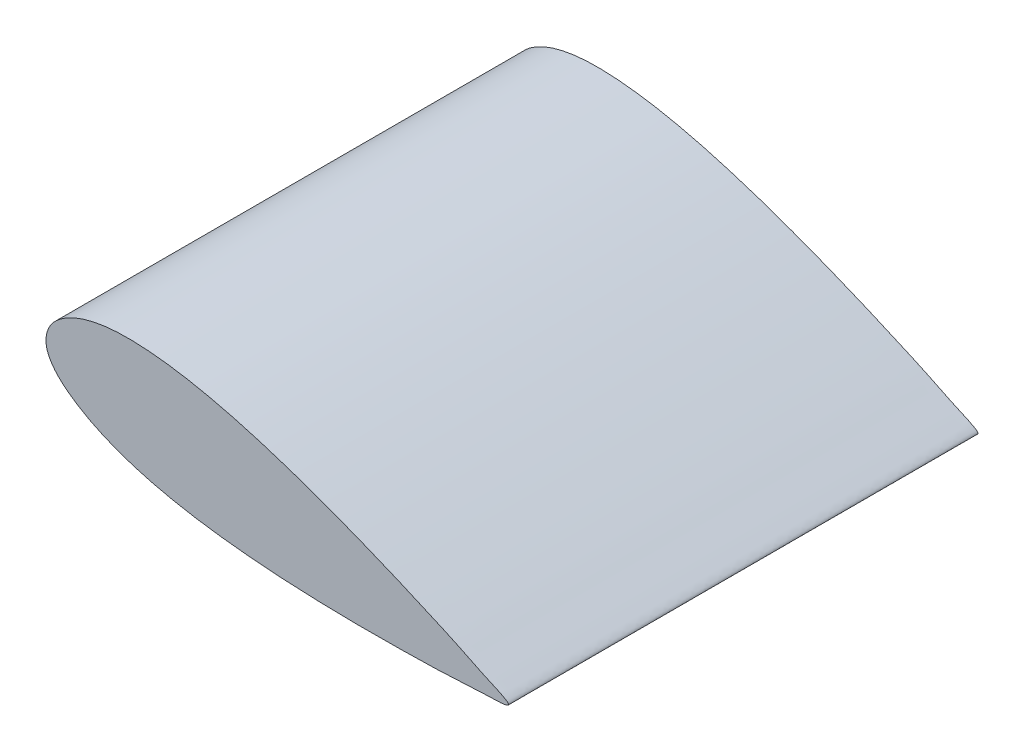
SolidWorks part; units mm, degrees
ref_plane "Front Plane"
ref_plane "Top Plane" through (0, 0, 0) normal (0, 1, 0) x (1, 0, 0)
ref_plane "Right Plane" through (0, 0, 0) normal (1, 0, 0) x (0, 0, -1)
curve "Krzywa1"
  spline degree 3 poles (0.9428, -0.0156, 0) (1.0287, -0.0006, 0) (0.9435, 0.0181, 0) (0.8883, 0.0354, 0) (0.8001, 0.0574, 0) (0.7023, 0.0802, 0) (0.6022, 0.1006, 0) (0.5027, 0.1176, 0) (0.4028, 0.1303, 0) (0.3194, 0.1358, 0) (0.2526, 0.1358, 0) (0.2015, 0.1329, 0) (0.1483, 0.1261, 0) (0.1024, 0.1145, 0) (0.0652, 0.0989, 0) (0.0372, 0.0821, 0) (0.0154, 0.0621, 0) (-0.0018, 0.0351, 0) (-0.005, -0.0015, 0) (0.0163, -0.0292, 0) (0.0392, -0.0467, 0) (0.0601, -0.0584, 0) (0.0834, -0.0687, 0) (0.1128, -0.0792, 0) (0.1506, -0.0894, 0) (0.198, -0.0977, 0) (0.2473, -0.1027, 0) (0.314, -0.1056, 0) (0.3976, -0.1038, 0) (0.4979, -0.0955, 0) (0.5981, -0.0829, 0) (0.699, -0.067, 0) (0.7977, -0.0485, 0) (0.8869, -0.0304, 0) (0.9428, -0.0156, 0) (1.0287, -0.0006, 0) (0.9435, 0.0181, 0) knots -0.097469 -0.04907 -0.024756 0 0.024751 0.04907 0.097468 0.145589 0.193458 0.241069 0.288432 0.335582 0.359147 0.382782 0.407745 0.434926 0.449379 0.46453 0.480955 0.490565 0.509531 0.528284 0.536925 0.550401 0.562004 0.572912 0.5945 0.61722 0.640856 0.664418 0.71157 0.758924 0.806536 0.854407 0.902531 0.95093 0.975244 1 1.024751 1.04907 1.097468 periodic
sketch "Szkic1" plane through (0, 0, 0) normal (0, 0, 1) x (1, 0, 0)
  spline S1 degree 3 poles (462.879, -89.5272) (506.4684, -89.6246) (466.1671, -73.0204) (440.4954, -59.7028) (398.9448, -41.2005) (352.7598, -21.4647) (305.2614, -2.7545) (257.7187, 14.2543) (209.6552, 29.1661) (169.0459, 39.1549) (136.1543, 44.9567) (110.7769, 47.9282) (83.9682, 49.2125) (60.3497, 47.4932) (40.7121, 43.018) (25.4276, 37.2245) (12.982, 29.2599) (2.1437, 17.4495) (-2.5962, -0.3238) (5.4857, -15.7707) (15.2524, -26.3774) (24.5213, -33.9922) (35.1194, -41.0578) (48.6741, -48.8102) (66.4116, -57.0816) (89.027, -65.3111) (112.8532, -72.0398) (145.4554, -79.2868) (186.7898, -85.6211) (236.8966, -90.2639) (287.3262, -92.7716) (338.3708, -93.6956) (388.5945, -93.1489) (434.0629, -91.9802) (462.879, -89.5272) (506.4684, -89.6246) (466.1671, -73.0204) knots -0.097469 -0.04907 -0.024756 0 0.024751 0.04907 0.097468 0.145589 0.193458 0.241069 0.288432 0.335582 0.359147 0.382782 0.407745 0.434926 0.449379 0.46453 0.480955 0.490565 0.509531 0.528284 0.536925 0.550401 0.562004 0.572912 0.5945 0.61722 0.640856 0.664418 0.71157 0.758924 0.806536 0.854407 0.902531 0.95093 0.975244 1 1.024751 1.04907 1.097468 only from (492.4039, -86.8241) to (492.4039, -86.8241)
extrude "Dodanie-wyciągnięcie1" add sketch "Szkic1" along normal blind 500
